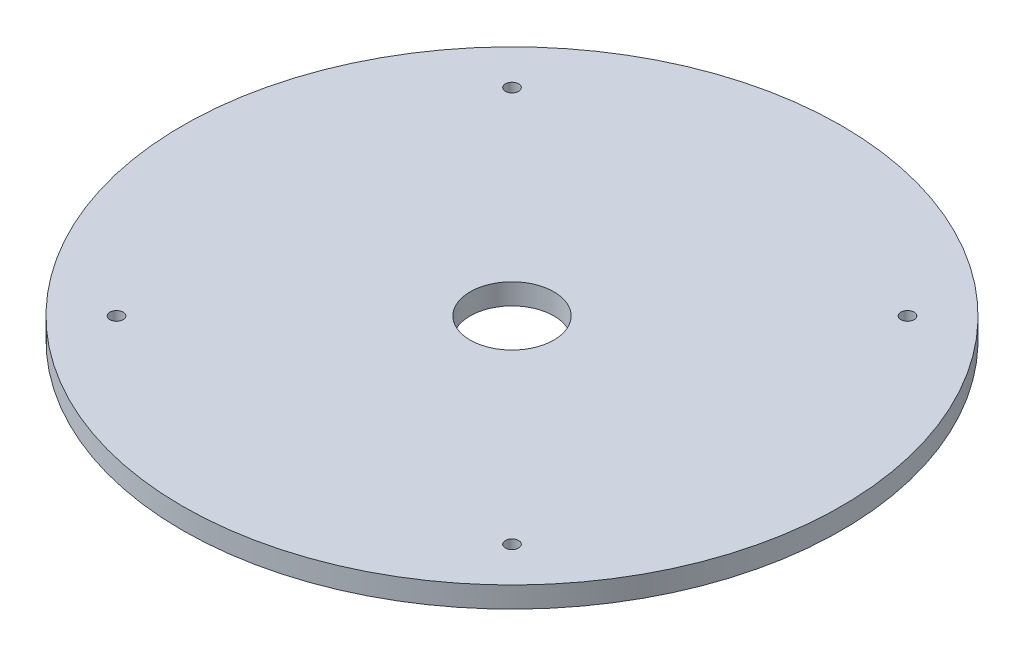
SolidWorks part; units mm, degrees
material "Acrylic (Medium-high impact)"
ref_plane "Front Plane" through (0, 0, 0) normal (0, 0, 1) x (1, 0, 0)
ref_plane "Top Plane" through (0, 0, 0) normal (0, 1, 0) x (1, 0, 0)
ref_plane "Right Plane" through (0, 0, 0) normal (1, 0, 0) x (0, 0, -1)
sketch "Sketch1" plane through (0, 0, 0) normal (0, 1, 0) x (1, 0, 0)
  line L0 (-30, 30) -> (30, -30) construction
  line L1 (-30, 30) -> (30, 30) construction
  line L6 (-30, 30) -> (-30, -30) construction
  line L7 (-30, -30) -> (30, -30) construction
  line L8 (30, 30) -> (30, -30) construction
  circle A0 centre (0, 0) radius 50
  circle A5 centre (-30, 30) radius 1
  circle A6 centre (30, 30) radius 1
  circle A7 centre (30, -30) radius 1
  circle A8 centre (-30, -30) radius 1
  circle A9 centre (0, 0) radius 6.35
  dimension "D1" = 100
  dimension "D3" = 2
  dimension "D4" = 12.7
  dimension "D2" = 60
extrude "Boss-Extrude1" add sketch "Sketch1" along normal blind 3.175
sketch "Sketch2" [suppressed] plane through (0, 3.175, 0) normal (0, 1, 0) x (1, 0, 0)
  line L0 (0, 36.3616) -> (0, -49963.6384) construction
  circle A0 centre (0, 40) radius 1.6
  circle A1 centre (0, 30) radius 1.6
  circle A2 centre (0, 20) radius 1.6
  dimension "D1" = 3.2
  dimension "D2" = 10
  dimension "D3" = 10
  dimension "D4" = 20
extrude "Cut-Extrude1" [suppressed] cut sketch "Sketch2" against normal up to next
pattern_circular "CirPattern1" [suppressed] count 12 over 360
